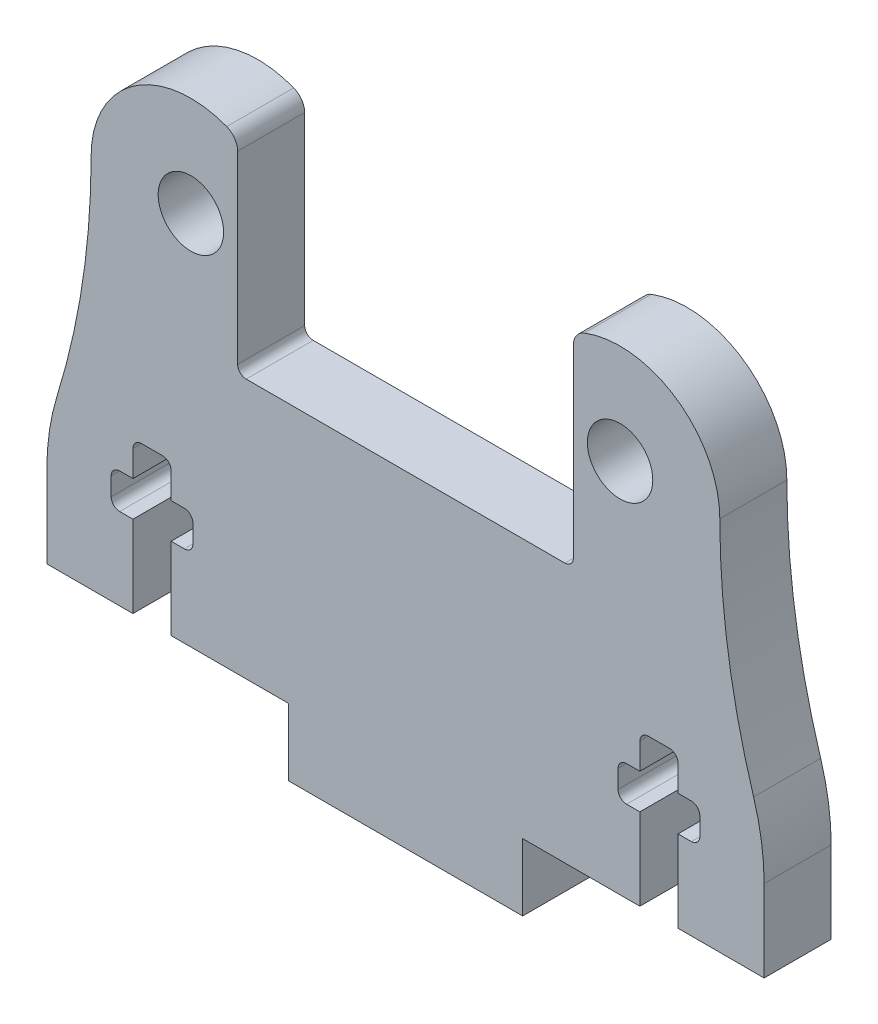
SolidWorks part; units mm, degrees
ref_plane "Alzado" through (0, 0, 0) normal (0, 0, 1) x (1, 0, 0)
ref_plane "Planta" through (0, 0, 0) normal (0, 1, 0) x (1, 0, 0)
ref_plane "Vista lateral" through (0, 0, 0) normal (1, 0, 0) x (0, 0, -1)
sketch "Croquis1" plane through (0, 0, 0) normal (0, 0, 1) x (1, 0, 0)
  line L0 (-10, 0) -> (10, 0) construction
  line L1 (5.461, 17.5) -> (5.461, 20.6242)
  line L2 (-10, 17.5) -> (10, 17.5)
  line L3 (-10, 17.5) -> (-10, -17.5)
  line L4 (-10, -17.5) -> (10, -17.5)
  line L5 (10, 17.5) -> (10, -17.5)
  line L6 (-5.461, -17.5) -> (5.461, -17.5)
  line L7 (-5.461, -17.5) -> (-5.461, -20.6242)
  line L8 (-5.461, -20.6242) -> (5.461, -20.6242)
  line L9 (5.461, -17.5) -> (5.461, -20.6242)
  line L10 (-5.461, 20.6242) -> (5.461, 20.6242)
  line L11 (-5.461, 17.5) -> (-5.461, 20.6242)
  line L12 (-5.461, 17.5) -> (5.461, 17.5)
  line L13 (0, 0) -> (0, -5.3975) construction
  line L14 (-7.4263, -5.3975) -> (7.4263, -5.3975)
  line L15 (-7.8232, -5.0006) -> (-7.8232, 5.0006)
  line L16 (-7.4263, 5.3975) -> (7.4263, 5.3975)
  line L17 (7.8232, -5.0006) -> (7.8232, 5.0006)
  line L18 (-7.8232, -5.3975) -> (7.8232, 5.3975) construction
  line L19 (-7.8232, 5.3975) -> (7.8232, -5.3975) construction
  line L20 (11.3189, -10.4388) -> (12.3031, -10.4388)
  line L21 (10.795, -17.5) -> (12.7, -17.5)
  line L29 (10.922, -10.8357) -> (10.922, -17.5)
  line L30 (10.922, -17.5) -> (12.7, -17.5)
  line L31 (12.7, -10.8357) -> (12.7, -17.5)
  line L32 (10.3029, -12.0517) -> (13.3191, -12.0517)
  line L33 (9.906, -12.4486) -> (9.906, -13.2931)
  line L34 (10.3029, -13.69) -> (13.3191, -13.69)
  line L35 (13.716, -12.4486) -> (13.716, -13.2931)
  line L36 (-16.7132, -17.5) -> (-16.7132, -13.69)
  line L37 (-9.906, -12.4486) -> (-9.906, -13.2931)
  line L38 (16.7132, -17.5) -> (-16.7132, -17.5)
  line L39 (-13.716, -12.4486) -> (-13.716, -13.2931)
  line L40 (-10.3029, -13.69) -> (-13.3191, -13.69)
  line L41 (-10.3029, -12.0517) -> (-13.3191, -12.0517)
  line L42 (-12.7, -10.8357) -> (-12.7, -17.5)
  line L43 (-10.922, -17.5) -> (-12.7, -17.5)
  line L44 (-10.922, -10.8357) -> (-10.922, -17.5)
  line L45 (-10.795, -17.5) -> (-12.7, -17.5)
  line L46 (-11.3189, -10.4388) -> (-12.3031, -10.4388)
  line L47 (-16.7132, -17.5) -> (16.7132, -17.5)
  line L48 (16.7132, -17.5) -> (16.7132, -13.69)
  circle A0 centre (-10, 0) radius 1.524
  circle A1 centre (10, 0) radius 1.524
  arc A2 (-10, 4.6482) -> (-10, -4.6482) centre (-10, 0) ccw
  arc A3 (-10, 8.9799) -> (-12.6837, 3.7952) centre (-16.35, 8.9799) cw
  arc A4 (10, 8.9799) -> (12.6837, 3.7952) centre (16.35, 8.9799) ccw
  arc A5 (10, 4.6482) -> (10, -4.6482) centre (10, 0) cw
  arc A6 (-16.7132, -13.69) -> (-16.2228, -10.4388) centre (-5.691, -13.69) cw
  arc A7 (-16.2228, -10.4388) -> (-14.6482, 0) centre (-50.0377, 0) ccw
  arc A8 (-7.4263, -5.3975) -> (-7.8232, -5.0006) centre (-7.4263, -5.0006) cw
  arc A9 (7.4263, -5.3975) -> (7.8232, -5.0006) centre (7.4263, -5.0006) ccw
  arc A10 (7.4263, 5.3975) -> (7.8232, 5.0006) centre (7.4263, 5.0006) cw
  arc A11 (-7.8232, 5.0006) -> (-7.4263, 5.3975) centre (-7.4263, 5.0006) cw
  circle A12 centre (11.811, -17.5) radius 1.016
  circle A13 centre (11.811, -11.3278) radius 0.889
  arc A14 (9.906, -13.2931) -> (10.3029, -13.69) centre (10.3029, -13.2931) ccw
  arc A15 (13.3191, -13.69) -> (13.716, -13.2931) centre (13.3191, -13.2931) ccw
  arc A16 (10.3029, -12.0517) -> (9.906, -12.4486) centre (10.3029, -12.4486) ccw
  arc A17 (13.3191, -12.0517) -> (13.716, -12.4486) centre (13.3191, -12.4486) cw
  arc A18 (11.3189, -10.4388) -> (10.922, -10.8357) centre (11.3189, -10.8357) ccw
  arc A19 (12.3031, -10.4388) -> (12.7, -10.8357) centre (12.3031, -10.8357) cw
  arc A20 (-12.3031, -10.4388) -> (-12.7, -10.8357) centre (-12.3031, -10.8357) ccw
  arc A21 (-11.3189, -10.4388) -> (-10.922, -10.8357) centre (-11.3189, -10.8357) cw
  arc A22 (-13.3191, -12.0517) -> (-13.716, -12.4486) centre (-13.3191, -12.4486) ccw
  arc A23 (-10.3029, -12.0517) -> (-9.906, -12.4486) centre (-10.3029, -12.4486) cw
  arc A24 (-13.3191, -13.69) -> (-13.716, -13.2931) centre (-13.3191, -13.2931) cw
  arc A25 (-9.906, -13.2931) -> (-10.3029, -13.69) centre (-10.3029, -13.2931) cw
  circle A26 centre (-11.811, -11.3278) radius 0.889
  circle A27 centre (-11.811, -17.5) radius 1.016
  arc A28 (16.2228, -10.4388) -> (14.6482, 0) centre (50.0377, 0) cw
  arc A29 (16.7132, -13.69) -> (16.2228, -10.4388) centre (5.691, -13.69) ccw
  circle A30 centre (-10, 0) radius 4.6482
  circle A31 centre (10, 0) radius 4.6482
  arc A32 (-8.3321, 4.3387) -> (-7.8232, 3.5978) centre (-8.6169, 3.5978) cw
  arc A33 (8.3321, 4.3387) -> (7.8232, 3.5978) centre (8.6169, 3.5978) ccw
  point P3 (0, 0)
  point P6 (-8.476, 0)
  point P7 (8.476, 0)
  point P8 (-11.524, 0)
  point P9 (11.524, 0)
  point P14 (0, 17.5)
  point P15 (0, -20.6242)
  point P19 (10, 0)
  point P28 (0, 0)
  point P75 (11.811, -13.69)
  point P76 (11.811, -17.5)
  dimension "D1" = 3.048
  dimension "D6" = 3.1242
  dimension "D7" = 6.35
  dimension "D11" = 0.3969
  dimension "D13" = 6.35
  dimension "D14" = 2.032
  dimension "D15" = 1.778
  dimension "D16" = 1.778
  dimension "D21" = 0.3969
  dimension "D22" = 2.9972
  dimension "D23" = 0.7937
  dimension "D2" = 20
  dimension "D3" = 23.048
  dimension "D4" = 35
  dimension "D5" = 3.1242
  dimension "D8" = 10.795
  dimension "D9" = 15.6464
  dimension "D10" = 10.922
  dimension "D12" = 20
  dimension "D17" = 7.0612
  dimension "D18" = 1.6129
  dimension "D19" = 1.6383
  dimension "D20" = 3.81
extrude "Saliente-Extruir1" add sketch "Croquis1" along normal blind 3.1242
